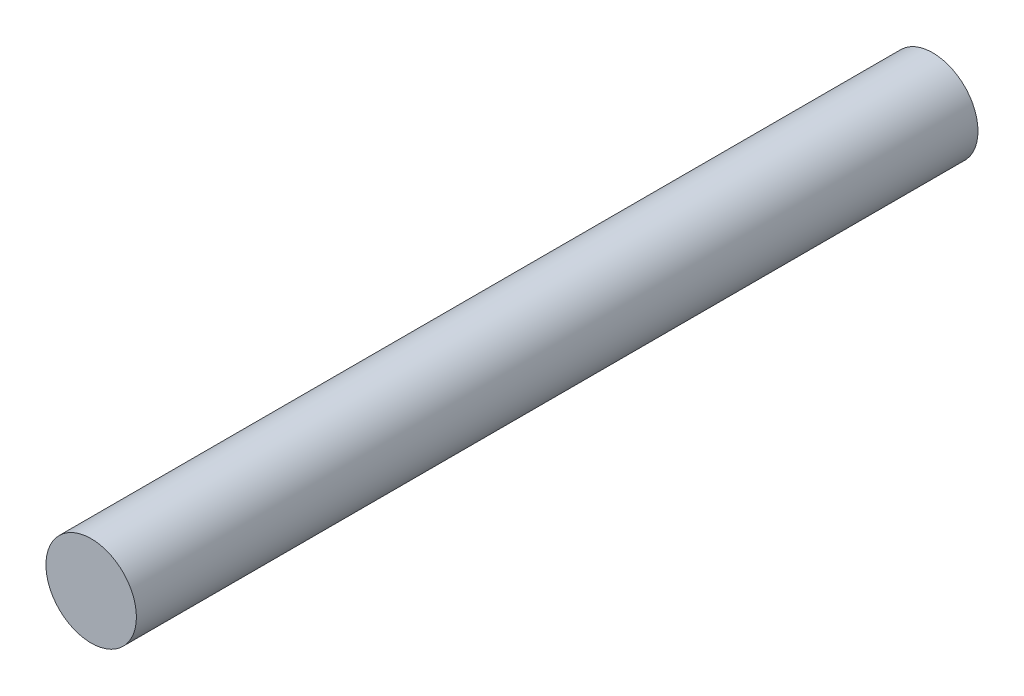
SolidWorks part; units mm, degrees
ref_plane "Front Plane" through (0, 0, 0) normal (0, 0, 1) x (1, 0, 0)
ref_plane "Top Plane" through (0, 0, 0) normal (0, 1, 0) x (1, 0, 0)
ref_plane "Right Plane" through (0, 0, 0) normal (1, 0, 0) x (0, 0, -1)
sketch "Sketch1" plane through (0, 0, 0) normal (0, 0, 1) x (1, 0, 0)
  circle A0 centre (0, 0) radius 2.5
  dimension "D1" = 5
extrude "Boss-Extrude1" add sketch "Sketch1" along normal blind 46.5
